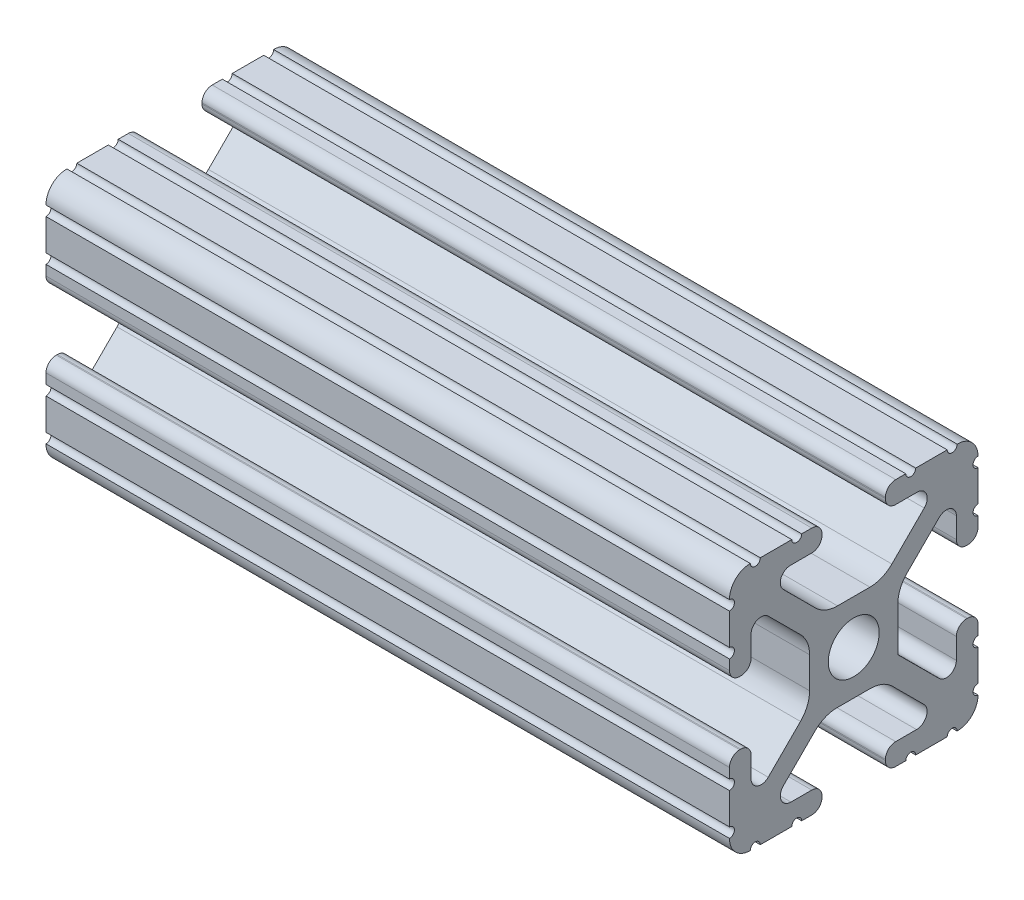
SolidWorks part; units mm, degrees
material "6061-T6 (SS)"
ref_plane "Front Plane" through (0, 0, 0) normal (0, 0, 1) x (1, 0, 0)
ref_plane "Top Plane" through (0, 0, 0) normal (0, 1, 0) x (1, 0, 0)
ref_plane "Right Plane" through (0, 0, 0) normal (1, 0, 0) x (0, 0, -1)
sketch "Sketch1" plane through (0, 0, 0) normal (1, 0, 0) x (0, 0, -1)
  line L0 (6.3331, -12.7) -> (9.5504, -12.7)
  line L1 (12.7, -9.5504) -> (12.7, -6.3331)
  line L2 (12.7, -5.3171) -> (12.7, -4.2875)
  line L3 (11.651, -3.2385) -> (11.5392, -3.2385)
  line L4 (10.4902, -4.2875) -> (10.4902, -6.4021)
  line L5 (8.7371, -7.1294) -> (4.5085, -2.9104)
  line L6 (4.5085, -2.9104) -> (4.5085, 1.5932)
  line L7 (5.441, 3.8408) -> (8.7371, 7.1294)
  line L8 (10.4902, 6.4021) -> (10.4902, 4.2875)
  line L9 (11.5392, 3.2385) -> (11.651, 3.2385)
  line L10 (12.7, 4.2875) -> (12.7, 5.3171)
  line L11 (12.7, 6.3331) -> (12.7, 9.5504)
  line L12 (9.5504, 12.7) -> (6.3331, 12.7)
  line L13 (5.3171, 12.7) -> (4.2875, 12.7)
  line L14 (3.2385, 11.651) -> (3.2385, 11.5392)
  line L15 (4.2875, 10.4902) -> (6.4768, 10.4902)
  line L16 (7.207, 8.7244) -> (3.8983, 5.4232)
  line L17 (1.6558, 4.4958) -> (-1.6558, 4.4958)
  line L18 (-3.8983, 5.4232) -> (-7.207, 8.7244)
  line L19 (-6.4768, 10.4902) -> (-4.2875, 10.4902)
  line L20 (-3.2385, 11.5392) -> (-3.2385, 11.651)
  line L21 (-4.2875, 12.7) -> (-5.3171, 12.7)
  line L22 (-6.3331, 12.7) -> (-9.5504, 12.7)
  line L23 (-12.7, 9.5504) -> (-12.7, 6.3331)
  line L24 (-12.7, 5.3171) -> (-12.7, 4.2875)
  line L25 (-11.651, 3.2385) -> (-11.5392, 3.2385)
  line L26 (-10.4902, 4.2875) -> (-10.4902, 6.4021)
  line L27 (-8.7371, 7.1294) -> (-5.441, 3.8408)
  line L28 (-4.5085, 1.5932) -> (-4.5085, -1.5932)
  line L29 (-5.441, -3.8408) -> (-8.7371, -7.1294)
  line L30 (-10.4902, -6.4021) -> (-10.4902, -4.2875)
  line L31 (-11.5392, -3.2385) -> (-11.651, -3.2385)
  line L32 (-12.7, -4.2875) -> (-12.7, -5.3171)
  line L33 (-12.7, -6.3331) -> (-12.7, -9.5504)
  line L34 (-9.5504, -12.7) -> (-6.3331, -12.7)
  line L35 (-5.3171, -12.7) -> (-4.2875, -12.7)
  line L36 (-3.2385, -11.651) -> (-3.2385, -11.5392)
  line L37 (-4.2875, -10.4902) -> (-6.4164, -10.4902)
  line L38 (-7.1797, -8.6452) -> (-3.9523, -5.4237)
  line L39 (-1.7093, -4.4958) -> (1.7093, -4.4958)
  line L40 (3.9523, -5.4237) -> (7.1797, -8.6452)
  line L41 (6.4164, -10.4902) -> (4.2875, -10.4902)
  line L42 (3.2385, -11.5392) -> (3.2385, -11.651)
  line L43 (4.2875, -12.7) -> (5.3171, -12.7)
  circle A0 centre (0, 0) radius 2.6035
  arc A1 (6.3331, -12.7) -> (5.3171, -12.7) centre (5.8251, -12.7) ccw
  arc A2 (10.5664, -12.6998) -> (9.5504, -12.7) centre (10.0584, -12.7) ccw
  arc A3 (10.5664, -12.6998) -> (12.6998, -10.5664) centre (10.5918, -10.5918) ccw
  arc A4 (12.7, -9.5504) -> (12.6998, -10.5664) centre (12.7, -10.0584) ccw
  arc A5 (12.7, -5.3171) -> (12.7, -6.3331) centre (12.7, -5.8251) ccw
  arc A6 (12.7, -4.2875) -> (11.651, -3.2385) centre (11.651, -4.2875) ccw
  arc A7 (11.5392, -3.2385) -> (10.4902, -4.2875) centre (11.5392, -4.2875) ccw
  arc A8 (8.7371, -7.1294) -> (10.4902, -6.4021) centre (9.4628, -6.4021) ccw
  arc A9 (5.441, 3.8408) -> (4.5085, 1.5932) centre (7.6835, 1.5932) ccw
  arc A10 (10.4902, 6.4021) -> (8.7371, 7.1294) centre (9.4628, 6.4021) ccw
  arc A11 (10.4902, 4.2875) -> (11.5392, 3.2385) centre (11.5392, 4.2875) ccw
  arc A12 (11.651, 3.2385) -> (12.7, 4.2875) centre (11.651, 4.2875) ccw
  arc A13 (12.7, 6.3331) -> (12.7, 5.3171) centre (12.7, 5.8251) ccw
  arc A14 (12.6998, 10.5664) -> (12.7, 9.5504) centre (12.7, 10.0584) ccw
  arc A15 (12.6998, 10.5664) -> (10.5664, 12.6998) centre (10.5918, 10.5918) ccw
  arc A16 (9.5504, 12.7) -> (10.5664, 12.6998) centre (10.0584, 12.7) ccw
  arc A17 (5.3171, 12.7) -> (6.3331, 12.7) centre (5.8251, 12.7) ccw
  arc A18 (4.2875, 12.7) -> (3.2385, 11.651) centre (4.2875, 11.651) ccw
  arc A19 (3.2385, 11.5392) -> (4.2875, 10.4902) centre (4.2875, 11.5392) ccw
  arc A20 (7.207, 8.7244) -> (6.4768, 10.4902) centre (6.4768, 9.4563) ccw
  arc A21 (1.6558, 4.4958) -> (3.8983, 5.4232) centre (1.6558, 7.6708) ccw
  arc A22 (-3.8983, 5.4232) -> (-1.6558, 4.4958) centre (-1.6558, 7.6708) ccw
  arc A23 (-6.4768, 10.4902) -> (-7.207, 8.7244) centre (-6.4768, 9.4563) ccw
  arc A24 (-4.2875, 10.4902) -> (-3.2385, 11.5392) centre (-4.2875, 11.5392) ccw
  arc A25 (-3.2385, 11.651) -> (-4.2875, 12.7) centre (-4.2875, 11.651) ccw
  arc A26 (-6.3331, 12.7) -> (-5.3171, 12.7) centre (-5.8251, 12.7) ccw
  arc A27 (-10.5664, 12.6998) -> (-9.5504, 12.7) centre (-10.0584, 12.7) ccw
  arc A28 (-10.5664, 12.6998) -> (-12.6998, 10.5664) centre (-10.5918, 10.5918) ccw
  arc A29 (-12.7, 9.5504) -> (-12.6998, 10.5664) centre (-12.7, 10.0584) ccw
  arc A30 (-12.7, 5.3171) -> (-12.7, 6.3331) centre (-12.7, 5.8251) ccw
  arc A31 (-12.7, 4.2875) -> (-11.651, 3.2385) centre (-11.651, 4.2875) ccw
  arc A32 (-11.5392, 3.2385) -> (-10.4902, 4.2875) centre (-11.5392, 4.2875) ccw
  arc A33 (-8.7371, 7.1294) -> (-10.4902, 6.4021) centre (-9.4628, 6.4021) ccw
  arc A34 (-4.5085, 1.5932) -> (-5.441, 3.8408) centre (-7.6835, 1.5932) ccw
  arc A35 (-5.441, -3.8408) -> (-4.5085, -1.5932) centre (-7.6835, -1.5932) ccw
  arc A36 (-10.4902, -6.4021) -> (-8.7371, -7.1294) centre (-9.4628, -6.4021) ccw
  arc A37 (-10.4902, -4.2875) -> (-11.5392, -3.2385) centre (-11.5392, -4.2875) ccw
  arc A38 (-11.651, -3.2385) -> (-12.7, -4.2875) centre (-11.651, -4.2875) ccw
  arc A39 (-12.7, -6.3331) -> (-12.7, -5.3171) centre (-12.7, -5.8251) ccw
  arc A40 (-12.6998, -10.5664) -> (-12.7, -9.5504) centre (-12.7, -10.0584) ccw
  arc A41 (-12.6998, -10.5664) -> (-10.5664, -12.6998) centre (-10.5918, -10.5918) ccw
  arc A42 (-9.5504, -12.7) -> (-10.5664, -12.6998) centre (-10.0584, -12.7) ccw
  arc A43 (-5.3171, -12.7) -> (-6.3331, -12.7) centre (-5.8251, -12.7) ccw
  arc A44 (-4.2875, -12.7) -> (-3.2385, -11.651) centre (-4.2875, -11.651) ccw
  arc A45 (-3.2385, -11.5392) -> (-4.2875, -10.4902) centre (-4.2875, -11.5392) ccw
  arc A46 (-7.1797, -8.6452) -> (-6.4164, -10.4902) centre (-6.4164, -9.4098) ccw
  arc A47 (-1.7093, -4.4958) -> (-3.9523, -5.4237) centre (-1.7093, -7.6708) ccw
  arc A48 (3.9523, -5.4237) -> (1.7093, -4.4958) centre (1.7093, -7.6708) ccw
  arc A49 (6.4164, -10.4902) -> (7.1797, -8.6452) centre (6.4164, -9.4098) ccw
  arc A50 (4.2875, -10.4902) -> (3.2385, -11.5392) centre (4.2875, -11.5392) ccw
  arc A51 (3.2385, -11.651) -> (4.2875, -12.7) centre (4.2875, -11.651) ccw
extrude "Boss-Extrude1" add sketch "Sketch1" along normal up to surface (69.85 mm away)
